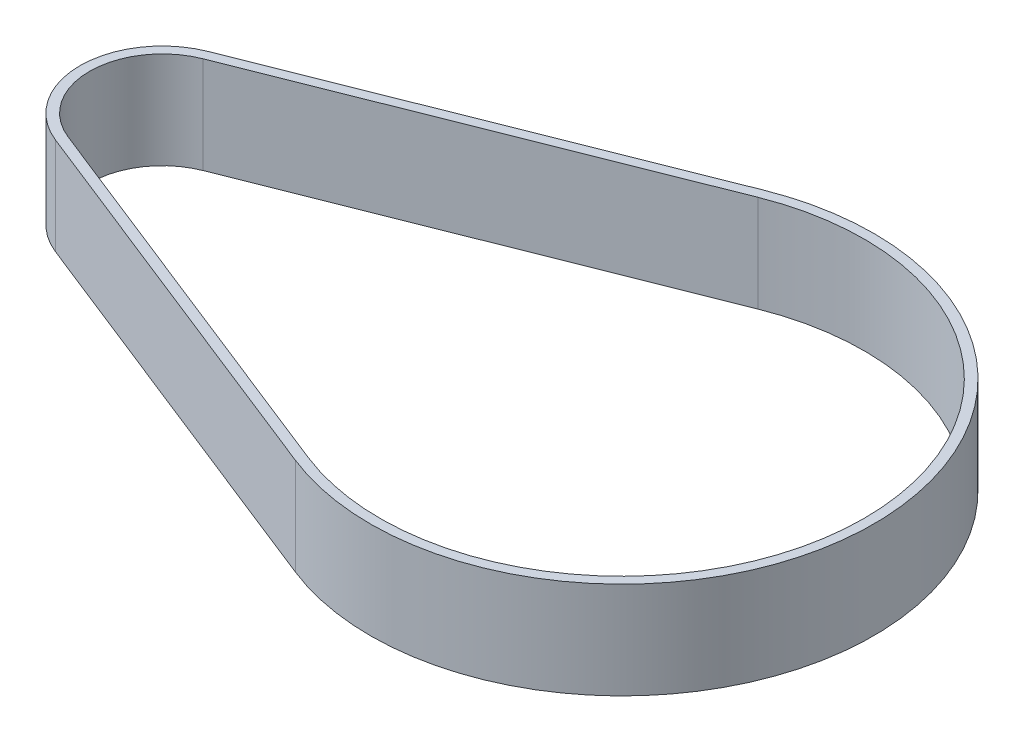
SolidWorks part; units mm, degrees
ref_plane "Front Plane" through (0, 0, 0) normal (0, 0, 1) x (1, 0, 0)
ref_plane "Top Plane" through (0, 0, 0) normal (0, 1, 0) x (1, 0, 0)
ref_plane "Right Plane" through (0, 0, 0) normal (1, 0, 0) x (0, 0, -1)
sketch "Sketch1" plane through (0, 0, 0) normal (0, 1, 0) x (1, 0, 0)
  line L1 (-48.0528, 6.9724) -> (-7.0002, 23.2415)
  line L2 (-48.0528, -6.9724) -> (-7.0002, -23.2415)
  line L3 (-48.4212, 7.9021) -> (-7.3686, 24.1711)
  line L4 (-48.4212, -7.9021) -> (-7.3686, -24.1711)
  arc A0 (-48.0528, 6.9724) -> (-48.0528, -6.9724) centre (-45.2896, 0) ccw
  arc A1 (-7.0002, -23.2415) -> (-7.0002, 23.2415) centre (2.2104, 0) ccw
  arc A2 (-7.3686, -24.1711) -> (-7.3686, 24.1711) centre (2.2104, 0) ccw
  arc A4 (-48.4212, 7.9021) -> (-48.4212, -7.9021) centre (-45.2896, 0) ccw
  point P5 (-52.7896, 0)
  point P6 (27.2104, 0)
  dimension "D1" = 50
  dimension "D2" = 15
  dimension "D3" = 80
extrude "Boss-Extrude1" add sketch "Sketch1" along normal blind 10
